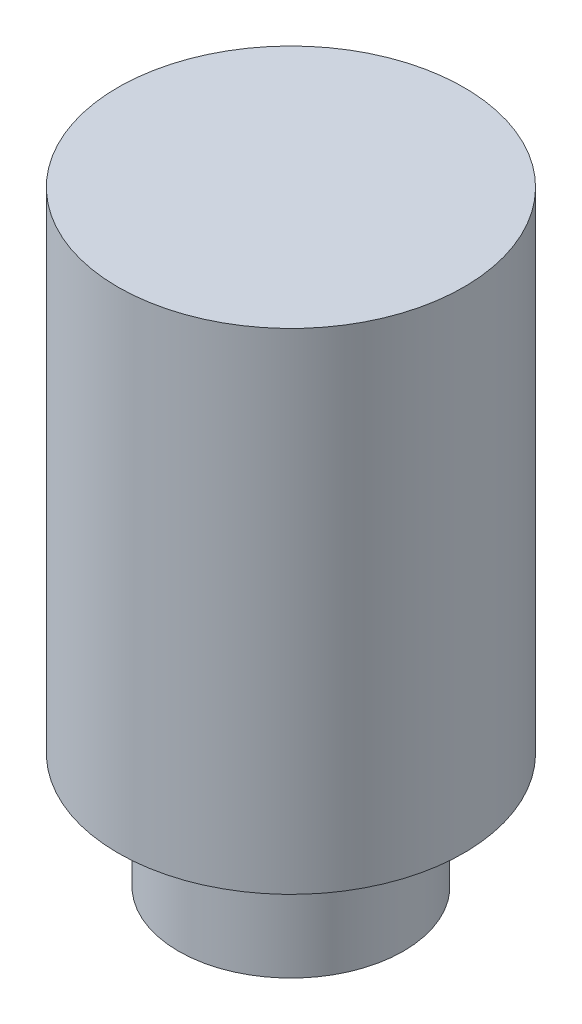
SolidWorks part; units mm, degrees
ref_plane "Спереди" through (0, 0, 0) normal (0, 0, 1) x (1, 0, 0)
ref_plane "Сверху" through (0, 0, 0) normal (0, 1, 0) x (1, 0, 0)
ref_plane "Справа" through (0, 0, 0) normal (1, 0, 0) x (0, 0, -1)
sketch "Эскиз1" plane through (0, 0, 0) normal (0, 1, 0) x (1, 0, 0)
  circle A0 centre (0, 0) radius 1.95
  dimension "D1" = 3.9
extrude "Бобышка-Вытянуть1" add sketch "Эскиз1" along normal blind 2
sketch "Эскиз2" plane through (0, 2, 0) normal (0, 1, 0) x (1, 0, 0)
  circle A0 centre (0, 0) radius 3
  dimension "D1" = 6
extrude "Бобышка-Вытянуть2" add sketch "Эскиз2" along normal blind 8.5
